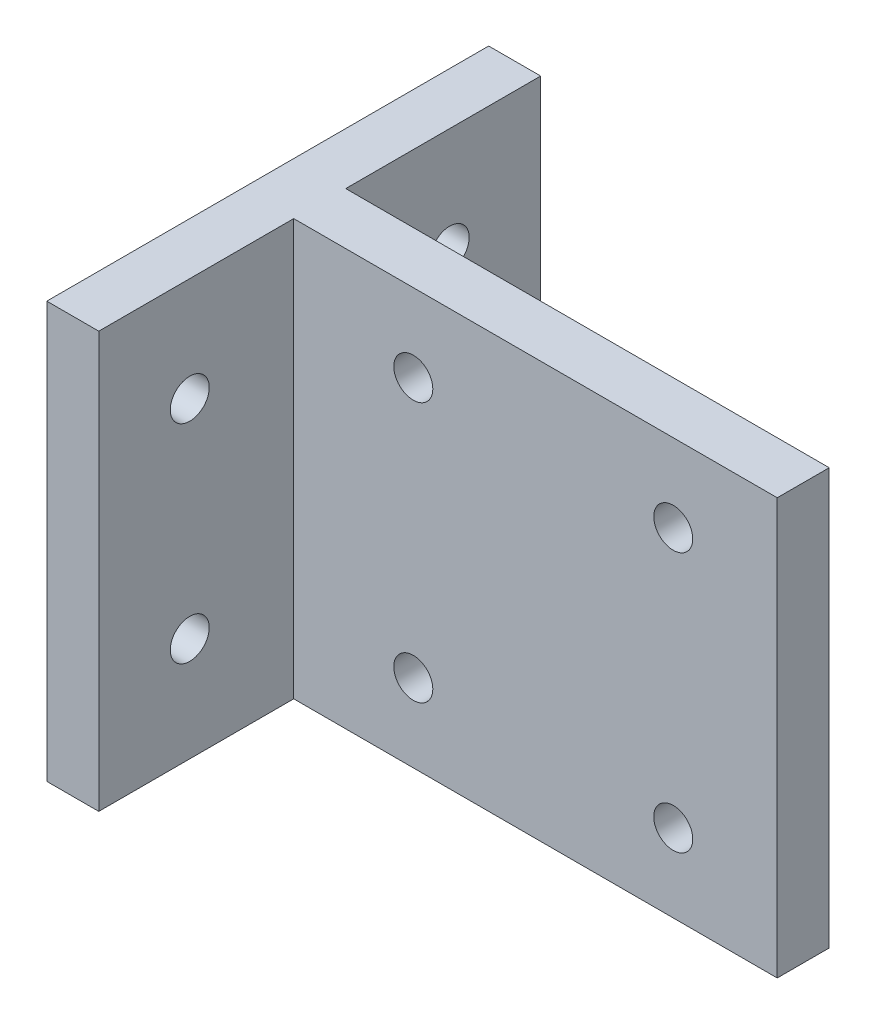
SolidWorks part; units mm, degrees
ref_plane "Спереди" through (0, 0, 0) normal (0, 0, 1) x (1, 0, 0)
ref_plane "Сверху" through (0, 0, 0) normal (0, 1, 0) x (1, 0, 0)
ref_plane "Справа" through (0, 0, 0) normal (1, 0, 0) x (0, 0, -1)
sketch "Эскиз1" plane through (0, 0, 0) normal (0, 0, 1) x (1, 0, 0)
  line L0 (0, 0) -> (36, 0)
  line L1 (0, 0) -> (0, 32)
  line L2 (36, 0) -> (36, 32)
  line L3 (0, 32) -> (36, 32)
  line L4 (18, 32) -> (18, 0) construction
  line L5 (36, 16) -> (0, 16) construction
  line L6 (8, 26) -> (8, 6) construction
  line L7 (8, 26) -> (28, 26) construction
  line L8 (28, 26) -> (28, 6) construction
  line L9 (28, 6) -> (8, 6) construction
  line L10 (8, 16) -> (28, 16) construction
  line L11 (18, 26) -> (18, 6) construction
  circle A0 centre (8, 26) radius 1.5
  circle A1 centre (28, 26) radius 1.5
  circle A2 centre (8, 6) radius 1.5
  circle A3 centre (28, 6) radius 1.5
  dimension "D1" = 20
  dimension "D2" = 20
  dimension "D3" = 3
  dimension "D4" = 3
  dimension "D5" = 3
  dimension "D6" = 3
  dimension "D7" = 32
  dimension "D8" = 36
extrude "Бобышка-Вытянуть1" add sketch "Эскиз1" along normal blind 4
sketch "Эскиз6" plane through (0, 32, 0) normal (0, 1, 0) x (1, 0, 0)
  line L0 (-5.2, -4) -> (-5.2, 24.8582) construction
  line L1 (36, -4) -> (0, -4) construction
  line L2 (36, -4) -> (36, 0) construction
  line L3 (-7.2, -4) -> (-7.2, 26.2382) construction
  dimension "D1" = 41.2
  dimension "D2" = 2
sketch "Эскиз7" plane through (0, 32, 0) normal (0, 1, 0) x (1, 0, 0)
  line L0 (0, 0) -> (-1.2, 0)
  line L1 (-1.2, 0) -> (-1.2, 15)
  line L3 (0, -4) -> (-1.2, -4)
  line L4 (-1.2, -4) -> (-1.2, -19)
  line L5 (-1.2, -19) -> (-5.2, -19)
  line L6 (-5.2, -19) -> (-5.2, 15)
  line L7 (-5.2, 15) -> (-1.2, 15)
  line L8 (-5.2, -4) -> (-5.2, 24.8582) construction
  line L9 (0, -4) -> (0, 0)
  dimension "D1" = 4
  dimension "D2" = 15
  dimension "D3" = 15
extrude "Бобышка-Вытянуть2" add sketch "Эскиз7" against normal up to surface (32 mm away) up to face at (18, 0, 2)
sketch "Эскиз8" plane through (-1.2, 0, 0) normal (1, 0, 0) x (0, 0, -1)
  line L0 (8, 24) -> (-12, 24) construction
  line L3 (8, 24) -> (8, 8) construction
  line L4 (-12, 24) -> (-12, 8) construction
  line L5 (8, 8) -> (-12, 8) construction
  line L6 (-4, 0) -> (-4, 32) construction
  line L7 (-4, 0) -> (-19, 0) construction
  line L8 (-19, 32) -> (-4, 32) construction
  circle A0 centre (8, 24) radius 1.5
  circle A1 centre (8, 8) radius 1.5
  circle A2 centre (-12, 8) radius 1.5
  circle A3 centre (-12, 24) radius 1.5
  dimension "D7" = 3
  dimension "D8" = 3
  dimension "D9" = 3
  dimension "D10" = 3
  dimension "D1" = 20
  dimension "D2" = 8
  dimension "D3" = 8
  dimension "D4" = 16
  dimension "D5" = 8
  dimension "D6" = 8
extrude "Вырез-Вытянуть1" cut sketch "Эскиз8" against normal through all
